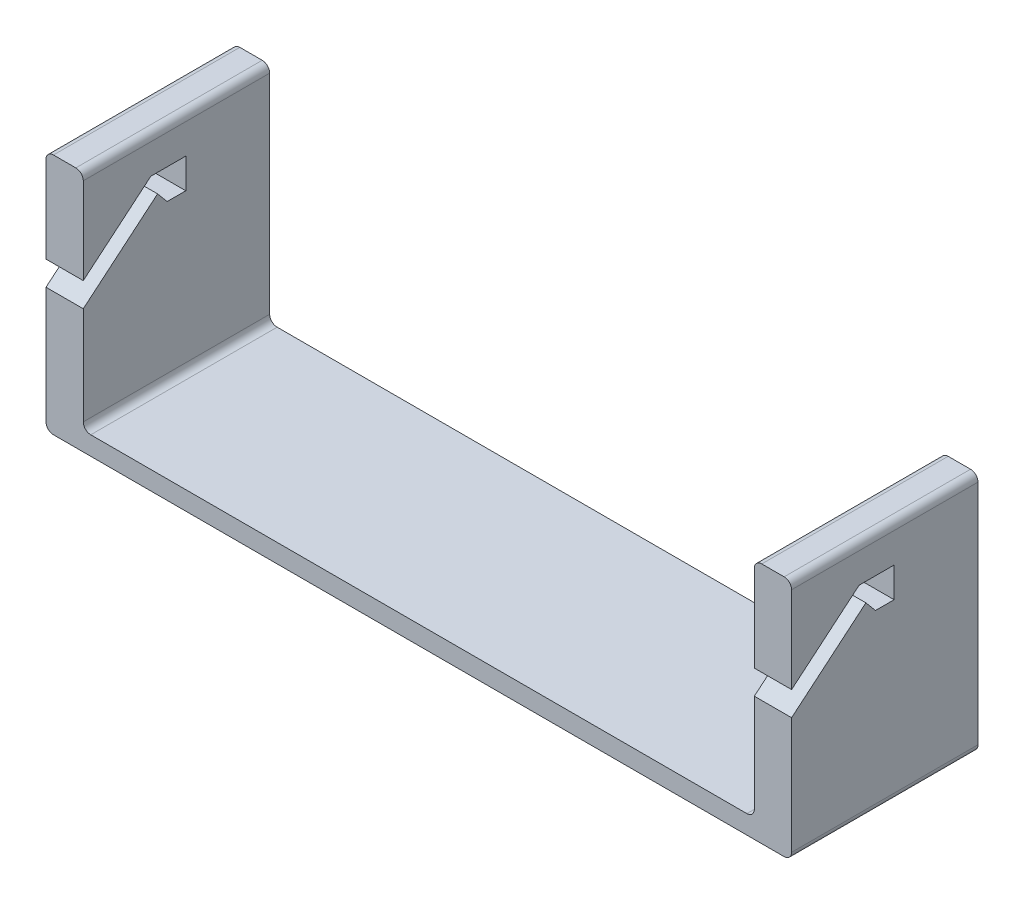
SolidWorks part; units mm, degrees
ref_plane "Front Plane" through (0, 0, 0) normal (0, 0, 1) x (1, 0, 0)
ref_plane "Top Plane" through (0, 0, 0) normal (0, 1, 0) x (1, 0, 0)
ref_plane "Right Plane" through (0, 0, 0) normal (1, 0, 0) x (0, 0, -1)
sketch "Sketch1" plane through (0, 0, 0) normal (0, 1, 0) x (1, 0, 0)
  line L1 (100, -25) -> (-100, -25)
  line L2 (100, -25) -> (100, 25)
  line L3 (100, 25) -> (-100, 25)
  line L4 (-100, -25) -> (-100, 25)
  line L5 (100, -25) -> (-100, 25) construction
  line L6 (100, 25) -> (-100, -25) construction
  point P0 (0, 0)
  dimension "D1" = 200
  dimension "D2" = 50
extrude "Boss-Extrude1" add sketch "Sketch1" along normal blind 5
sketch "Sketch2" plane through (-100, 0, 0) normal (-1, 0, 0) x (0, 0, 1)
  line L0 (25, 5) -> (25, 65)
  line L1 (25, 65) -> (-25, 65)
  line L2 (-25, 65) -> (-25, 5)
  line L3 (-25, 5) -> (25, 5)
  point P3 (0, 65)
  dimension "D1" = 60
  dimension "D2" = 50
extrude "Boss-Extrude2" add sketch "Sketch2" against normal blind 10
sketch "Sketch3" plane through (-100, 0, 0) normal (-1, 0, 0) x (0, 0, 1)
  line L0 (25, 39.8047) -> (6.891, 55)
  line L1 (25, 0) -> (25, 65) construction
  line L2 (6.891, 55) -> (-2.5, 55)
  line L3 (-2.5, 55) -> (-2.5, 46.9358)
  line L4 (-2.5, 46.9358) -> (2.5, 46.9358)
  line L5 (2.5, 46.9358) -> (5.0712, 50)
  line L6 (5.0712, 50) -> (25, 33.2777)
  line L7 (25, 33.2777) -> (25, 39.8047)
  line L8 (25, 65) -> (25, 0) construction
  line L9 (-25, 0) -> (25, 0) construction
  point P13 (0, 46.9358)
  dimension "D1" = 5
  dimension "D2" = 5
  dimension "D3" = 5
  dimension "D4" = 40
  dimension "D5" = 55
  dimension "D6" = 4
extrude "Cut-Extrude1" cut sketch "Sketch3" against normal through all both
mirror "Mirror1" about plane through (0, 0, 0) normal (1, 0, 0) of "Cut-Extrude1", "Boss-Extrude2"
fillet "Fillet1" radius 2 8 edges at (-100, 0, 0) (100, 0, 0) (90, 65, 0) (100, 65, 0) (-100, 65, 0) (-90, 65, 0) (-90, 5, 0) (90, 5, 0)
